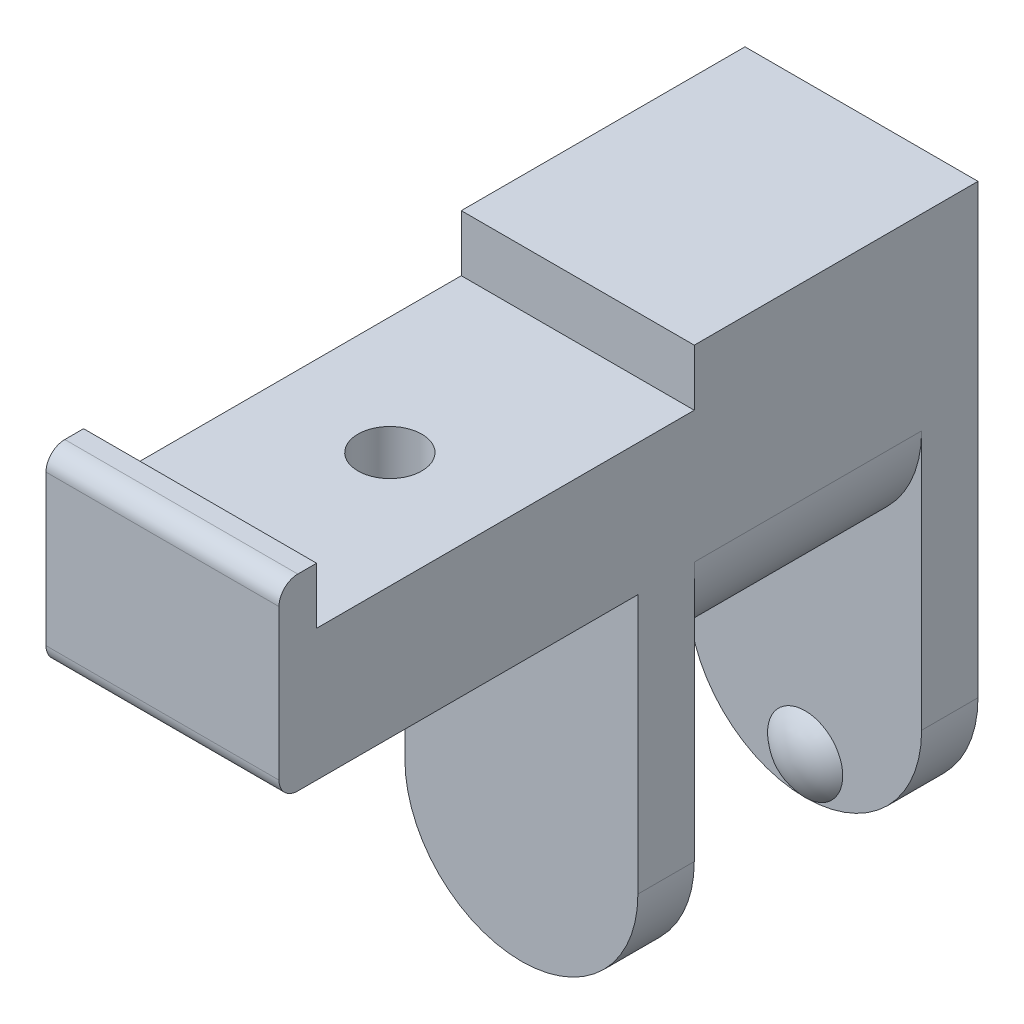
SolidWorks part; units mm, degrees
ref_plane "Спереди" through (0, 0, 0) normal (0, 0, 1) x (1, 0, 0)
ref_plane "Сверху" through (0, 0, 0) normal (0, 1, 0) x (1, 0, 0)
ref_plane "Справа" through (0, 0, 0) normal (1, 0, 0) x (0, 0, -1)
sketch "Эскиз2" plane through (0, 0, 0) normal (1, 0, 0) x (0, 0, -1)
  line L0 (12.1, -20) -> (15.1, -20)
  line L1 (15.1, -20) -> (15.1, 10)
  line L2 (15.1, 10) -> (0, 10)
  line L3 (-22.1, 10) -> (-22.1, 0)
  line L4 (-22.1, 0) -> (-3, 0)
  line L5 (-3, 0) -> (-3, -20)
  line L6 (-3, -20) -> (0, -20)
  line L7 (0, -20) -> (0, 0)
  line L8 (0, 0) -> (12.1, 0)
  line L9 (12.1, 0) -> (12.1, -20)
  line L10 (0, -8) -> (12.1, -8)
  line L11 (-20.1, 10) -> (-20.1, 7)
  line L12 (-20.1, 7) -> (0, 7)
  line L13 (0, 7) -> (0, 10)
  line L14 (-20.1, 10) -> (-22.1, 10)
  dimension "D1" = 30
  dimension "D2" = 20
  dimension "D3" = 3
  dimension "D4" = 12.1
  dimension "D5" = 8
  dimension "D6" = 10
  dimension "D7" = 20.1
  dimension "D8" = 2
  dimension "D9" = 3
extrude "Бобышка-Вытянуть1" add sketch "Эскиз2" along normal blind 12.4 contours L11 L14 L3 L4 L5 L6 L7 L8 L9 L0 L1 L2 L13 L12 | L7 L10 L9 L8
sketch "Эскиз3" plane through (0, 0, 0) normal (0, 0, 1) x (1, 0, 0)
  line L0 (0, 0) -> (12.4, 0) construction
  line L1 (0, 0) -> (-4.3102, 0)
  line L2 (-4.3102, 0) -> (-4.3102, -10.1582)
  line L3 (-4.3102, -10.1582) -> (16.7843, -10.1582)
  line L4 (16.7843, -10.1582) -> (16.7843, 0)
  line L5 (16.7843, 0) -> (12.4, 0)
  arc A0 (0, 0) -> (12.4, 0) centre (6.2, 0) ccw
  dimension "D1" = 6.2
  dimension "D2" = 16.7843
  dimension "D3" = 4.3102
  dimension "D4" = 10.1582
extrude "Вырез-Вытянуть1" cut sketch "Эскиз3" against normal up to surface (12.1 mm away) up to face at (6.2, -14, -12.1)
sketch "Эскиз4" plane through (0, 0, 0) normal (0, 0, 1) x (1, 0, 0)
  line L0 (0, -13.8) -> (12.4, -13.8) construction
  line L1 (0, 0) -> (0, -20) construction
  line L2 (12.4, -20) -> (12.4, 0) construction
  line L3 (12.4, -20) -> (0, -20) construction
  line L4 (0, -13.8) -> (-4.5292, -13.8)
  line L5 (-4.5292, -13.8) -> (-4.5292, -23.0327)
  line L6 (-4.5292, -23.0327) -> (17.4573, -23.0327)
  line L7 (17.4573, -23.0327) -> (17.4573, -13.8)
  line L8 (17.4573, -13.8) -> (12.4, -13.8)
  arc A0 (0, -13.8) -> (12.4, -13.8) centre (6.2, -13.8) ccw
  dimension "D1" = 17.4573
  dimension "D2" = 4.5292
  dimension "D3" = 23.0327
extrude "Вырез-Вытянуть2" cut sketch "Эскиз4" against normal through all both and the other way through all
hole_wizard "Отверстие с зазором M31" positions "Эскиз7" profile "Эскиз8" hole size "M3" standard "IS"
sketch "Эскиз7" plane through (0, 7, 0) normal (0, 1, 0) x (1, 0, 0)
  line L0 (12.4, 0) -> (0, 0) construction
  line L1 (0, -20.1) -> (0, 0) construction
  point P0 (6.25, -10.05)
  dimension "D1" = 10.05
  dimension "D2" = 6.25
sketch "Эскиз8" plane through (6.25, 7, 10.05) normal (1, 0, 0) x (0, 0, 1)
  line L0 (0, 0) -> (0, 11.0215)
  line L1 (0, 11.0215) -> (1.7, 10)
  line L2 (1.7, 10) -> (1.7, 0)
  line L5 (1.7, 0) -> (0, 0)
  line L10 (0, 11.0215) -> (-1.7, 10) construction
  line L11 (0, -6.35) -> (0, 107.95) construction
  dimension "Диаметр отверстия" = 3.4
  dimension "Глубина отверстия" = 10
  dimension "Угол заточки сверла" = 118
fillet "Скругление1" radius 1 2 edges at (6.2, 0, 22.1) (6.2, 10, 22.1)
ref_plane "Плоскость1" through (6.2, 0, 0) normal (1, 0, 0) x (0, 0, -1)
sketch "Эскиз9" plane through (6.2, 0, 0) normal (1, 0, 0) x (0, 0, -1)
  line L4 (12.1, -20) -> (12.1, -18)
  line L5 (12.1, 0) -> (12.1, -13.8) construction
  line L6 (11.3, -18) -> (12.1, -18)
  arc A0 (12.1, -20) -> (11.3, -18) centre (14.2, -18) cw
  point P7 (11.8051, -19.4291)
  point P8 (11.5, -18.3109)
  point P9 (11.5, -18.7555)
  point P10 (11.5, -18.0475)
  point P11 (12.1, -20)
  dimension "D1" = 2
  dimension "D2" = 0.8
revolve "Повернуть1" add sketch "Эскиз9" angle 360 about L6
